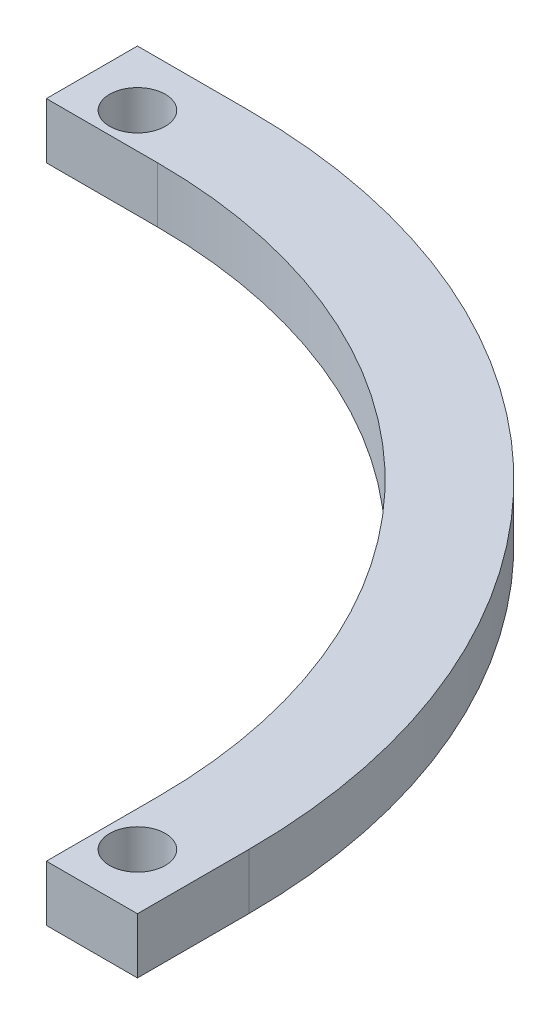
SolidWorks part; units mm, degrees
ref_plane "Front Plane" through (0, 0, 0) normal (0, 0, 1) x (1, 0, 0)
ref_plane "Top Plane" through (0, 0, 0) normal (0, 1, 0) x (1, 0, 0)
ref_plane "Right Plane" through (0, 0, 0) normal (1, 0, 0) x (0, 0, -1)
sketch "Sketch1" plane through (0, 0, 0) normal (0, 1, 0) x (1, 0, 0)
  line L0 (47.5, 0) -> (47.5, -10)
  line L1 (47.5, -10) -> (57.5, -10)
  line L2 (57.5, -10) -> (57.5, 0)
  line L3 (0, 0) -> (62.064, 62.064) construction
  line L4 (0, 0) -> (99.8594, 0) construction
  line L5 (-10, 57.5) -> (0, 57.5)
  line L6 (-10, 47.5) -> (-10, 57.5)
  line L7 (0, 47.5) -> (-10, 47.5)
  arc A0 (47.5, 0) -> (0, 47.5) centre (0, 0) ccw
  arc A1 (57.5, 0) -> (0, 57.5) centre (0, 0) ccw
  circle A2 centre (52.5, -5) radius 2.5
  circle A3 centre (-5, 52.5) radius 2.5
  dimension "D1" = 47.5
  dimension "D3" = 57.5
  dimension "D5" = 5
  dimension "D2" = 45
  dimension "D4" = 10
extrude "Boss-Extrude2" add sketch "Sketch1" along normal blind 5
sketch "Sketch3" plane through (0, 5, 0) normal (0, 1, 0) x (1, 0, 0)
  line L0 (49.32, 0) -> (49.32, -10)
  line L1 (47.5, -10) -> (57.5, -10) construction
  line L2 (0, 49.32) -> (-10, 49.32)
  line L3 (-10, 57.5) -> (-10, 47.5) construction
  arc A0 (0, 49.32) -> (49.32, 0) centre (0, 0) cw
  dimension "D1" = 49.32
split "Split1" trim tools "Sketch3" bodies to split 102 resulting bodies 103
